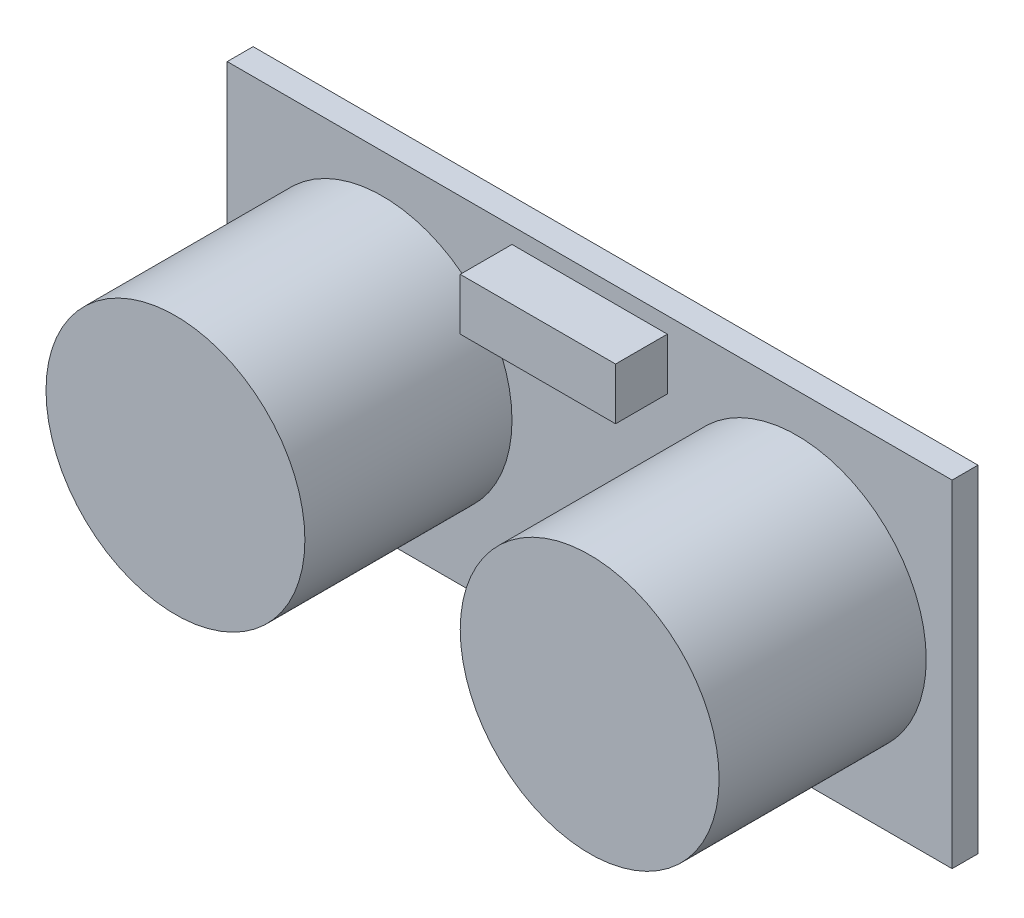
SolidWorks part; units mm, degrees
ref_plane "Front Plane" through (0, 0, 0) normal (0, 0, 1) x (1, 0, 0)
ref_plane "Top Plane" through (0, 0, 0) normal (0, 1, 0) x (1, 0, 0)
ref_plane "Right Plane" through (0, 0, 0) normal (1, 0, 0) x (0, 0, -1)
sketch "Sketch1" plane through (0, 0, 0) normal (0, 0, 1) x (1, 0, 0)
  line L1 (-22.225, -10.3187) -> (22.225, -10.3187)
  line L2 (-22.225, -10.3187) -> (-22.225, 10.3188)
  line L3 (-22.225, 10.3188) -> (22.225, 10.3188)
  line L4 (22.225, -10.3187) -> (22.225, 10.3188)
  line L5 (-22.225, -10.3187) -> (22.225, 10.3188) construction
  line L6 (-22.225, 10.3188) -> (22.225, -10.3187) construction
  point P0 (0, 0)
  dimension "D1" = 44.45
  dimension "D2" = 20.6375
extrude "Boss-Extrude1" add sketch "Sketch1" along normal blind 1.5875
sketch "Sketch2" plane through (0, 0, 1.5875) normal (0, 0, 1) x (1, 0, 0)
  line L1 (0, 10.3188) -> (0, 0) construction
  line L2 (22.225, 10.3188) -> (-22.225, 10.3188) construction
  line L3 (0, 0) -> (-22.225, 0) construction
  line L4 (-22.225, 10.3188) -> (-22.225, -10.3187) construction
  circle A0 centre (-12.7, 0) radius 7.9375
  dimension "D1" = 15.875
  dimension "D3" = 12.7
  dimension "D2" = 22.225
extrude "Boss-Extrude2" add sketch "Sketch2" along normal blind 12.7
mirror "Mirror1" about plane through (0, 0, 0) normal (1, 0, 0) of "Boss-Extrude2"
sketch "Sketch3" plane through (0, 0, 1.5875) normal (0, 0, 1) x (1, 0, 0)
  line L0 (0, 10.3188) -> (0, -10.5042) construction
  line L1 (22.225, 10.3188) -> (-22.225, 10.3188) construction
  line L3 (-4.7625, 6.1629) -> (4.7625, 6.1629)
  line L4 (-4.7625, 6.1629) -> (-4.7625, 9.3379)
  line L5 (-4.7625, 9.3379) -> (4.7625, 9.3379)
  line L6 (4.7625, 6.1629) -> (4.7625, 9.3379)
  line L7 (-4.7625, 6.1629) -> (4.7625, 9.3379) construction
  line L8 (-4.7625, 9.3379) -> (4.7625, 6.1629) construction
  point P5 (0, 7.7504)
  dimension "D1" = 9.525
  dimension "D2" = 3.175
extrude "Boss-Extrude3" add sketch "Sketch3" along normal blind 3.175
